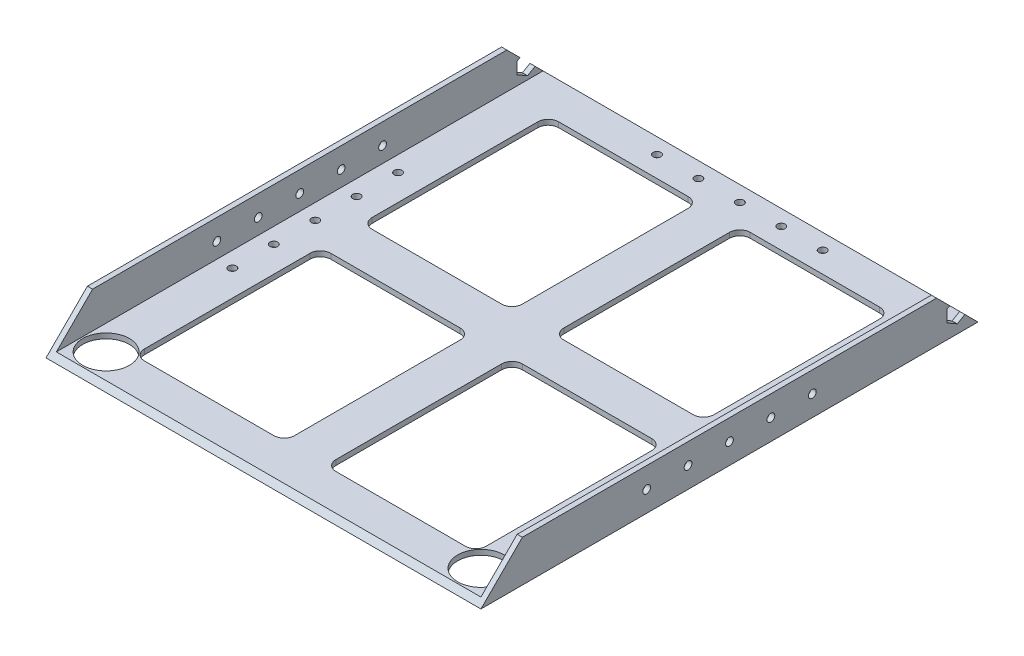
SolidWorks part; units mm, degrees
ref_plane "Front Plane" through (0, 0, 0) normal (0, 0, 1) x (1, 0, 0)
ref_plane "Top Plane" through (0, 0, 0) normal (0, 1, 0) x (1, 0, 0)
ref_plane "Right Plane" through (0, 0, 0) normal (1, 0, 0) x (0, 0, -1)
sketch "Sketch1" plane through (0, 0, 0) normal (0, 1, 0) x (1, 0, 0)
  line L1 (-86.5214, 188.3975) -> (180.1786, 188.3975)
  line L2 (-86.5214, 188.3975) -> (-86.5214, -116.4025)
  line L3 (-86.5214, -116.4025) -> (180.1786, -116.4025)
  line L4 (180.1786, 188.3975) -> (180.1786, -116.4025)
  dimension "D1" = 266.7
  dimension "D2" = 304.8
extrude "Boss-Extrude1" add sketch "Sketch1" along normal blind 25.4
sketch "Sketch2" plane through (0, 0, 116.4025) normal (0, 0, 1) x (1, 0, 0)
  line L0 (-86.5214, 25.4) -> (180.1786, 25.4) construction
  line L1 (-83.3464, 25.4) -> (177.0036, 25.4)
  line L2 (-83.3464, 25.4) -> (-83.3464, 3.175)
  line L3 (-83.3464, 3.175) -> (177.0036, 3.175)
  line L4 (177.0036, 25.4) -> (177.0036, 3.175)
  line L5 (-86.5214, 0) -> (180.1786, 0) construction
  line L6 (-86.5214, 25.4) -> (-86.5214, 0) construction
  line L7 (180.1786, 25.4) -> (180.1786, 0) construction
  dimension "D1" = 3.175
  dimension "D2" = 3.175
  dimension "D3" = 3.175
extrude "Cut-Extrude1" cut sketch "Sketch2" against normal blind 12700
sketch "Sketch3" plane through (0, 3.175, 0) normal (0, 1, 0) x (1, 0, 0)
  line L0 (-83.3464, -116.4025) -> (177.0036, -116.4025) construction
  line L1 (145.2536, -91.0025) -> (65.8786, -91.0025)
  line L2 (151.6036, -84.6525) -> (151.6036, 16.9475)
  line L3 (145.2536, 23.2975) -> (65.8786, 23.2975)
  line L4 (59.5286, -84.6525) -> (59.5286, 16.9475)
  line L5 (27.7786, -91.0025) -> (-51.5964, -91.0025)
  line L6 (34.1286, -84.6525) -> (34.1286, 16.9475)
  line L7 (27.7786, 23.2975) -> (-51.5964, 23.2975)
  line L8 (-57.9464, -84.6525) -> (-57.9464, 16.9475)
  line L9 (145.2536, 48.6975) -> (65.8786, 48.6975)
  line L10 (151.6036, 55.0475) -> (151.6036, 156.6475)
  line L11 (145.2536, 162.9975) -> (65.8786, 162.9975)
  line L12 (59.5286, 55.0475) -> (59.5286, 156.6475)
  line L13 (27.7786, 48.6975) -> (-51.5964, 48.6975)
  line L14 (34.1286, 55.0475) -> (34.1286, 156.6475)
  line L15 (27.7786, 162.9975) -> (-51.5964, 162.9975)
  line L16 (-57.9464, 55.0475) -> (-57.9464, 156.6475)
  line L17 (-83.3464, 188.3975) -> (-83.3464, -116.4025) construction
  line L18 (-83.3464, 188.3975) -> (177.0036, 188.3975) construction
  line L21 (177.0036, -116.4025) -> (177.0036, 188.3975) construction
  arc A0 (151.6036, -84.6525) -> (145.2536, -91.0025) centre (145.2536, -84.6525) cw
  arc A1 (151.6036, 16.9475) -> (145.2536, 23.2975) centre (145.2536, 16.9475) ccw
  arc A2 (65.8786, 23.2975) -> (59.5286, 16.9475) centre (65.8786, 16.9475) ccw
  arc A3 (65.8786, -91.0025) -> (59.5286, -84.6525) centre (65.8786, -84.6525) cw
  arc A4 (34.1286, -84.6525) -> (27.7786, -91.0025) centre (27.7786, -84.6525) cw
  arc A5 (34.1286, 16.9475) -> (27.7786, 23.2975) centre (27.7786, 16.9475) ccw
  arc A6 (-51.5964, 23.2975) -> (-57.9464, 16.9475) centre (-51.5964, 16.9475) ccw
  arc A7 (-57.9464, -84.6525) -> (-51.5964, -91.0025) centre (-51.5964, -84.6525) ccw
  arc A8 (34.1286, 55.0475) -> (27.7786, 48.6975) centre (27.7786, 55.0475) cw
  arc A9 (-51.5964, 48.6975) -> (-57.9464, 55.0475) centre (-51.5964, 55.0475) cw
  arc A10 (-57.9464, 156.6475) -> (-51.5964, 162.9975) centre (-51.5964, 156.6475) cw
  arc A11 (27.7786, 162.9975) -> (34.1286, 156.6475) centre (27.7786, 156.6475) cw
  arc A12 (65.8786, 162.9975) -> (59.5286, 156.6475) centre (65.8786, 156.6475) ccw
  arc A13 (59.5286, 55.0475) -> (65.8786, 48.6975) centre (65.8786, 55.0475) ccw
  arc A14 (145.2536, 48.6975) -> (151.6036, 55.0475) centre (145.2536, 55.0475) ccw
  arc A15 (145.2536, 162.9975) -> (151.6036, 156.6475) centre (145.2536, 156.6475) cw
  dimension "D13" = 6.35
  dimension "D14" = 6.35
  dimension "D15" = 6.35
  dimension "D16" = 6.35
  dimension "D1" = 25.4
  dimension "D2" = 25.4
  dimension "D3" = 25.4
  dimension "D4" = 25.4
  dimension "D5" = 25.4
  dimension "D6" = 25.4
  dimension "D7" = 25.4
  dimension "D8" = 25.4
  dimension "D9" = 25.4
  dimension "D10" = 25.4
  dimension "D12" = 25.4
extrude "Cut-Extrude2" cut sketch "Sketch3" against normal blind 12700 contours A3 L1 A0 L2 A1 L3 A2 L4 | A15 L11 A12 L12 A13 L9 A14 L10 | A11 L15 A10 L16 A9 L13 A8 L14 | L8 A7 L5 A4 L6 A5 L7 A6
sketch "Sketch4" plane through (180.1786, 0, 0) normal (1, 0, 0) x (0, 0, -1)
  line L0 (162.9975, 25.4) -> (188.3975, 0)
  line L1 (-116.4025, 25.4) -> (188.3975, 25.4) construction
  line L2 (188.3975, 25.4) -> (188.3975, 0) construction
  line L3 (188.3975, 0) -> (188.3975, 25.4)
  line L4 (188.3975, 25.4) -> (162.9975, 25.4)
  line L5 (-116.4025, 0) -> (188.3975, 0) construction
  line L6 (-116.4025, 0) -> (-91.0025, 25.4)
  line L7 (-91.0025, 25.4) -> (-116.4025, 25.4)
  line L8 (-116.4025, 25.4) -> (-116.4025, 0)
  dimension "D1" = 25.4
  dimension "D2" = 45
  dimension "D3" = 35.921
  dimension "D4" = 25.4
  dimension "D5" = 45
extrude "Cut-Extrude10" cut sketch "Sketch4" against normal blind 12700
sketch "Sketch5" plane through (180.1786, 0, 0) normal (1, 0, 0) x (0, 0, -1)
  line L0 (-91.0025, 25.4) -> (162.9975, 25.4) construction
  line L1 (162.9975, 25.4) -> (188.3975, 0) construction
  circle A0 centre (86.7975, 12.7) radius 2.3813
  circle A1 centre (35.9975, 12.7) radius 2.3813
  circle A2 centre (61.3975, 12.7) radius 2.3813
  circle A3 centre (10.5975, 12.7) radius 2.3812
  circle A4 centre (-14.8025, 12.7) radius 2.3813
  point P12 (35.9975, 25.4)
  point P15 (175.6975, 12.7)
  dimension "D5" = 4.7625
  dimension "D1" = 25.4
  dimension "D2" = 25.4
  dimension "D3" = 25.4
  dimension "D4" = 25.4
extrude "Cut-Extrude11" cut sketch "Sketch5" against normal through all
sketch "Sketch6" plane through (0, 3.175, 0) normal (0, 1, 0) x (1, 0, 0)
  line L0 (177.0036, 175.6975) -> (-83.3464, 175.6975) construction
  line L1 (177.0036, 185.2225) -> (177.0036, -113.2275) construction
  line L2 (-83.3464, 185.2225) -> (-83.3464, -113.2275) construction
  line L3 (180.1786, 188.3975) -> (-86.5214, 188.3975) construction
  circle A0 centre (46.8286, 175.6975) radius 2.3812
  circle A1 centre (21.4286, 175.6975) radius 2.3813
  circle A2 centre (-3.9714, 175.6975) radius 2.3812
  circle A3 centre (72.2286, 175.6975) radius 2.3813
  circle A4 centre (97.6286, 175.6975) radius 2.3813
  dimension "D2" = 25.4
  dimension "D3" = 25.4
  dimension "D4" = 25.4
  dimension "D6" = 4.7625
  dimension "D1" = 12.7
  dimension "D5" = 25.4
extrude "Cut-Extrude12" cut sketch "Sketch6" against normal through all
sketch "Sketch7" plane through (0, 3.175, 0) normal (0, 1, 0) x (1, 0, 0)
  line L0 (46.8286, 185.2225) -> (46.8286, -113.2275) construction
  line L1 (177.0036, 185.2225) -> (-83.3464, 185.2225) construction
  line L2 (-83.3464, -113.2275) -> (177.0036, -113.2275) construction
  line L3 (-83.3464, 185.2225) -> (-83.3464, -113.2275) construction
  circle A0 centre (-68.1064, -97.9875) radius 14.2875
  circle A1 centre (161.7636, -97.9875) radius 14.2875
  dimension "D1" = 28.575
  dimension "D2" = 15.24
  dimension "D3" = 15.24
extrude "Cut-Extrude13" cut sketch "Sketch7" against normal blind 3.175
sketch "Sketch8" plane through (0, 3.175, 0) normal (0, 1, 0) x (1, 0, 0)
  line L0 (46.8286, -113.2275) -> (46.8286, 185.2225) construction
  line L1 (-83.3464, -113.2275) -> (177.0036, -113.2275) construction
  line L2 (177.0036, 185.2225) -> (-83.3464, 185.2225) construction
  line L3 (167.4786, 86.7975) -> (167.4786, -14.8025) construction
  line L5 (180.1786, -116.4025) -> (180.1786, 188.3975) construction
  circle A0 centre (167.4786, 35.9975) radius 2.3813
  circle A1 centre (167.4786, 61.3975) radius 2.3813
  circle A2 centre (167.4786, 86.7975) radius 2.3813
  circle A3 centre (167.4786, 10.5975) radius 2.3813
  circle A4 centre (167.4786, -14.8025) radius 2.3813
  circle A5 centre (-73.8214, -14.8025) radius 2.3813
  circle A6 centre (-73.8214, 10.5975) radius 2.3813
  circle A7 centre (-73.8214, 35.9975) radius 2.3813
  circle A8 centre (-73.8214, 61.3975) radius 2.3813
  circle A9 centre (-73.8214, 86.7975) radius 2.3813
  point P26 (46.8286, 35.9975)
  dimension "D1" = 25.4
  dimension "D2" = 4.7625
  dimension "D3" = 25.4
  dimension "D4" = 25.4
  dimension "D5" = 12.7
extrude "Cut-Extrude14" cut sketch "Sketch8" against normal through all
sketch "Sketch9" plane through (-86.5214, 0, 0) normal (-1, 0, 0) x (0, 0, 1)
  line L0 (-175.6975, 12.7) -> (-175.6975, 20.0323) construction
  line L1 (-175.6975, 20.0323) -> (-182.0475, 16.3662)
  line L2 (-182.0475, 16.3662) -> (-182.0475, 9.0338)
  line L3 (-182.0475, 9.0338) -> (-175.6975, 5.3677)
  line L4 (-175.6975, 5.3677) -> (-169.3475, 9.0338)
  line L5 (-169.3475, 9.0338) -> (-169.3475, 16.3662)
  line L6 (-169.3475, 16.3662) -> (-175.6975, 20.0323)
  line L7 (-188.3975, 0) -> (116.4025, 0) construction
  circle A0 centre (-175.6975, 12.7) radius 6.35 construction
  dimension "D1" = 12.7
  dimension "D2" = 12.7
  dimension "D3" = 12.7
extrude "Cut-Extrude15" cut sketch "Sketch9" against normal through all contours L1 L2 L3 L4 L5 L6
equation "\"D2@Sketch5\"=\"D1@Sketch5\""
equation "\"D3@Sketch5\"=\"D1@Sketch5\""
equation "\"D4@Sketch5\"=\"D1@Sketch5\""
equation "\"D3@Sketch6\"=\"D2@Sketch6\""
equation "\"D4@Sketch6\"=\"D2@Sketch6\""
equation "\"D5@Sketch6\"=\"D2@Sketch6\""
